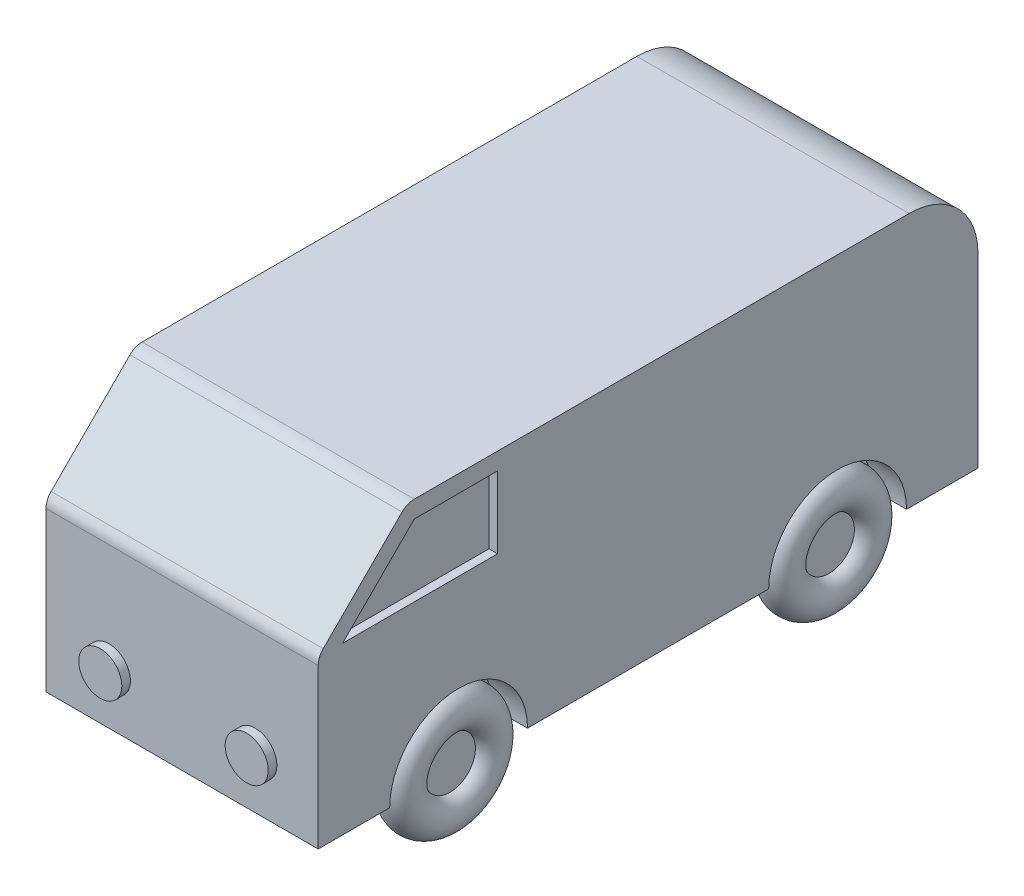
SolidWorks part; units mm, degrees
ref_plane "Front Plane" through (0, 0, 0) normal (0, 0, 1) x (1, 0, 0)
ref_plane "Top Plane" through (0, 0, 0) normal (0, 1, 0) x (1, 0, 0)
ref_plane "Right Plane" through (0, 0, 0) normal (1, 0, 0) x (0, 0, -1)
sketch "Sketch1" plane through (0, 0, 0) normal (1, 0, 0) x (0, 0, -1)
  line L0 (-191.5, 0) -> (0, 0)
  line L1 (0, 0) -> (191.5, 0)
  line L2 (191.5, 0) -> (191.5, 108)
  line L3 (151.5, 148) -> (-139.86, 148)
  line L5 (-191.5, 96.36) -> (-191.5, 0)
  line L6 (-191.5, 96.36) -> (-139.86, 148)
  arc A0 (191.5, 108) -> (151.5, 148) centre (151.5, 108) ccw
  point P7 (179.7843, 136.2843)
  dimension "D5" = 45
  dimension "D1" = 191.5
  dimension "D2" = 191.5
  dimension "D3" = 148
  dimension "D4" = 96.36
  dimension "D6" = 40
extrude "Boss-Extrude1" add sketch "Sketch1" along normal mid plane 158 contours L6 L3 A0 L2 L1 L0 L5
sketch "Sketch2" plane through (0, 0, 191.5) normal (0, 0, 1) x (1, 0, 0)
  line L0 (79, 0) -> (-79, 0) construction
  line L1 (-79, 96.36) -> (-79, 0) construction
  circle A0 centre (-42.5, 30) radius 12.5
  circle A1 centre (42.5, 30) radius 12.5
  dimension "D1" = 30
  dimension "D2" = 30
  dimension "D3" = 25
  dimension "D4" = 25
  dimension "D6" = 36.5
  dimension "D5" = 85
extrude "Boss-Extrude2" add sketch "Sketch2" along normal blind 5
sketch "Sketch3" plane through (-79, 0, 0) normal (-1, 0, 0) x (0, 0, 1)
  line L0 (191.5, 0) -> (-191.5, 0) construction
  circle A0 centre (-110, 0) radius 40
  circle A1 centre (110, 0) radius 40
  dimension "D1" = 80
  dimension "D2" = 80
  dimension "D3" = 220
  dimension "D4" = 110
extrude "Cut-Extrude1" cut sketch "Sketch3" against normal blind 20
mirror "Mirror1" about plane through (0, 0, 0) normal (1, 0, 0) of "Cut-Extrude1"
sketch "Sketch4" plane through (0, 0, 0) normal (0, 1, 0) x (1, 0, 0)
  line L0 (-59, 110) -> (-105.3411, 110) construction
  line L1 (-59, 150) -> (-59, 70) construction
  line L2 (-59, 110) -> (-59, 135)
  line L4 (-59, 110) -> (-74, 110)
  line L5 (-74, 110) -> (-74, 124.753)
  arc A0 (-59, 135) -> (-74, 124.753) centre (-70, 135) ccw
  dimension "D3" = 22
  dimension "D1" = 25
  dimension "D4" = 15
revolve "Revolve1" add sketch "Sketch4" angle 360 about L0
mirror "Mirror5" about plane through (0, 0, 0) normal (0, 0, 1) of "Revolve1"
mirror "Mirror6" about plane through (0, 0, 0) normal (1, 0, 0) of "Mirror5", "Revolve1"
sketch "Sketch5" plane through (-79, 0, 0) normal (-1, 0, 0) x (0, 0, 1)
  line L0 (135.7179, 138) -> (177.3579, 96.36)
  line L1 (177.3579, 96.36) -> (87.3579, 96.36)
  line L2 (87.3579, 96.36) -> (87.3579, 138)
  line L3 (87.3579, 138) -> (135.7179, 138)
  line L4 (191.5, 96.36) -> (139.86, 148) construction
  line L5 (-151.5, 148) -> (139.86, 148) construction
  dimension "D1" = 10
  dimension "D2" = 90
  dimension "D3" = 41.64
  dimension "D4" = 10
  dimension "D5" = 10
extrude "Cut-Extrude2" cut sketch "Sketch5" against normal blind 5
sketch "Sketch6" plane through (79, 0, 0) normal (1, 0, 0) x (0, 0, -1)
  line L0 (-177.3579, 96.36) -> (-135.7179, 138)
  line L1 (-135.7179, 138) -> (-87.3579, 138)
  line L2 (-87.3579, 138) -> (-87.3579, 96.36)
  line L3 (-87.3579, 96.36) -> (-177.3579, 96.36)
  line L4 (-191.5, 96.36) -> (-139.86, 148) construction
  line L5 (151.5, 148) -> (-139.86, 148) construction
  dimension "D1" = 10
  dimension "D2" = 10
  dimension "D3" = 41.64
  dimension "D4" = 90
extrude "Cut-Extrude3" cut sketch "Sketch6" against normal blind 5 contours L3 L0 L1 L2
fillet "Fillet1" radius 10 1 edges at (0, 96.36, 191.5)
fillet "Fillet2" radius 10 1 edges at (0, 148, 139.86)
